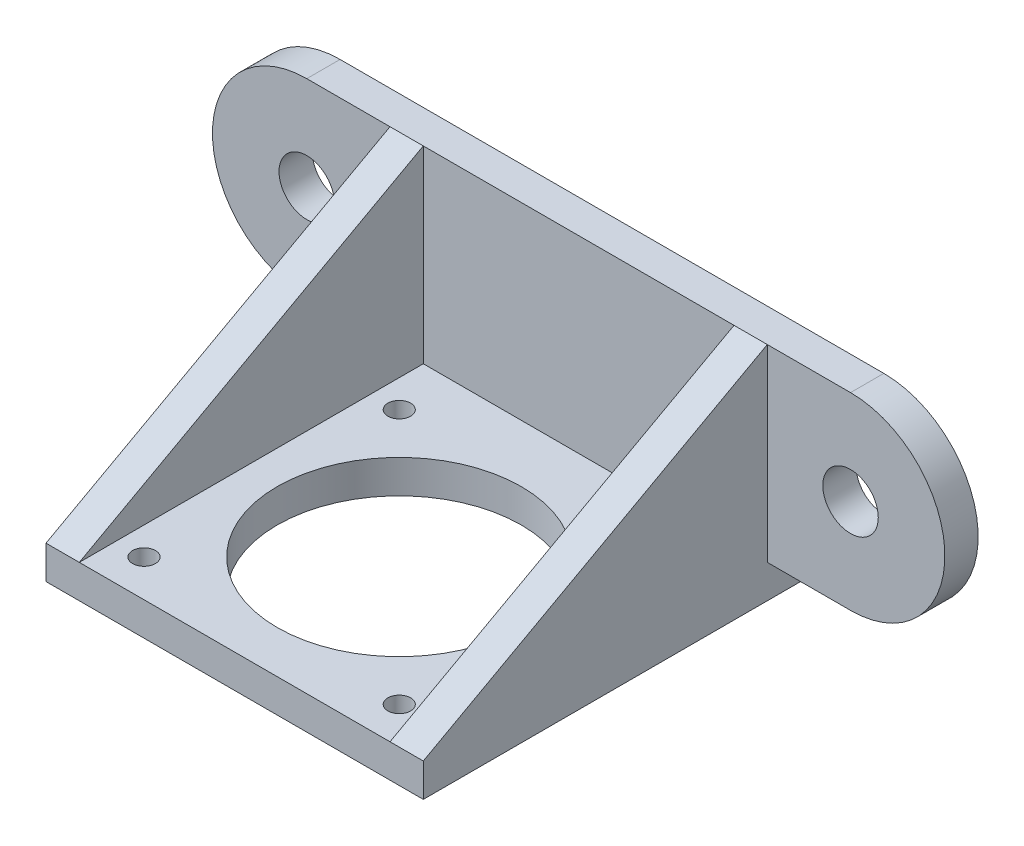
SolidWorks part; units mm, degrees
ref_plane "Front Plane" through (0, 0, 0) normal (0, 0, 1) x (1, 0, 0)
ref_plane "Top Plane" through (0, 0, 0) normal (0, 1, 0) x (1, 0, 0)
ref_plane "Right Plane" through (0, 0, 0) normal (1, 0, 0) x (0, 0, -1)
sketch "Sketch2" plane through (0, 0, 0) normal (1, 0, 0) x (0, 0, -1)
  line L0 (0, 0) -> (0, 20)
  line L1 (0, 0) -> (-34, 0)
  line L2 (-3, 3) -> (-3, 20)
  line L3 (-3, 3) -> (-34, 3)
  line L4 (0, 20) -> (-3, 20)
  line L5 (-34, 0) -> (-34, 3)
  dimension "D1" = 20
  dimension "D2" = 34
  dimension "D3" = 3
extrude "Boss-Extrude2" add sketch "Sketch2" along normal mid plane 34
sketch "Sketch5" plane through (17, 0, 0) normal (1, 0, 0) x (0, 0, -1)
  line L0 (-34, 3) -> (-3, 20)
  line L1 (-34, 3) -> (-34, 0) construction
  line L2 (-3, 3) -> (-34, 3) construction
rib "Rib2" sketch "Sketch5" sketch "Sketch5" thickness 3 extrusion direction parallel to sketch draft on no parameters "D1"=3
sketch "Sketch6" plane through (0, 0, 0) normal (0, 0, 1) x (1, 0, 0)
  line L0 (17, 0) -> (17, 20) construction
  line L1 (17, 20) -> (24.5, 20)
  line L2 (14, 3) -> (-17, 3) construction
  line L3 (14, 3) -> (-17, 3) construction
  line L4 (17, 3) -> (24.5, 3)
  line L5 (17, 3) -> (17, 20)
  circle A0 centre (24.5, 11.5) radius 2.5
  arc A1 (24.5, 20) -> (24.5, 3) centre (24.5, 11.5) cw
  dimension "D1" = 5
  dimension "D2" = 7.5
extrude "Boss-Extrude3" add sketch "Sketch6" along normal blind 3
mirror "Mirror1" about plane through (0, 0, 0) normal (1, 0, 0) of "Rib2", "Boss-Extrude3"
sketch "Sketch8" plane through (0, 3, 0) normal (0, 1, 0) x (1, 0, 0)
  line B0 (14, -30.668) -> (14, -7.668)
  line B1 (11.5, -5.168) -> (-11.5, -5.168)
  line B2 (-14, -7.668) -> (-14, -30.668)
  line B3 (-11.5, -33.168) -> (11.5, -33.168)
  arc B4 (14, -7.668) -> (11.5, -5.168) centre (11.5, -7.668) ccw
  arc B5 (-11.5, -5.168) -> (-14, -7.668) centre (-11.5, -7.668) ccw
  arc B6 (-14, -30.668) -> (-11.5, -33.168) centre (-11.5, -30.668) ccw
  arc B7 (11.5, -33.168) -> (14, -30.668) centre (11.5, -30.668) ccw
  arc B8 (11, -19.168) -> (-11, -19.168) centre (0, -19.168) ccw
  arc B9 (-11, -19.168) -> (11, -19.168) centre (0, -19.168) ccw
  arc B10 (-12.525, -30.668) -> (-10.475, -30.668) centre (-11.5, -30.668) ccw
  arc B11 (-10.475, -30.668) -> (-12.525, -30.668) centre (-11.5, -30.668) ccw
  arc B12 (10.475, -30.668) -> (12.525, -30.668) centre (11.5, -30.668) ccw
  arc B13 (12.525, -30.668) -> (10.475, -30.668) centre (11.5, -30.668) ccw
  arc B14 (10.475, -7.668) -> (12.525, -7.668) centre (11.5, -7.668) ccw
  arc B15 (12.525, -7.668) -> (10.475, -7.668) centre (11.5, -7.668) ccw
  arc B16 (-10.475, -7.668) -> (-12.525, -7.668) centre (-11.5, -7.668) ccw
  arc B17 (-12.525, -7.668) -> (-10.475, -7.668) centre (-11.5, -7.668) ccw
  dimension "D1" = 117.5
sketch_block_instance "Block-nema11-1"
sketch_block "Block-nema11"
extrude "Cut-Extrude1" cut sketch "Sketch8" against normal up to surface (3 mm away) contours B8 B9 | B16 B17 | B10 B11 | B14 B15 | B12 B13 up to face at (0, 0, 17)
